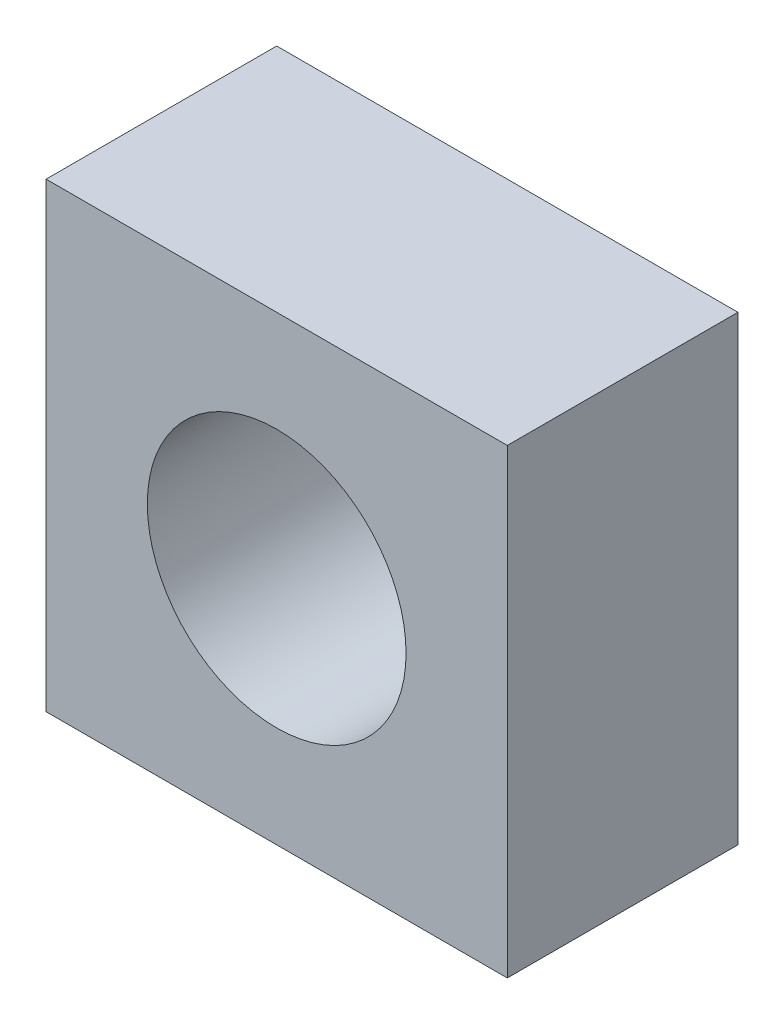
SolidWorks part; units mm, degrees
ref_plane "Front Plane" through (0, 0, 0) normal (0, 0, 1) x (1, 0, 0)
ref_plane "Top Plane" through (0, 0, 0) normal (0, 1, 0) x (1, 0, 0)
ref_plane "Right Plane" through (0, 0, 0) normal (1, 0, 0) x (0, 0, -1)
sketch "Sketch1" plane through (0, 0, 0) normal (0, 0, 1) x (1, 0, 0)
  line L1 (-20, -20) -> (20, -20)
  line L2 (-20, -20) -> (-20, 20)
  line L3 (-20, 20) -> (20, 20)
  line L4 (20, -20) -> (20, 20)
  line L5 (0, 20) -> (0, -20) construction
  line L6 (-20, 0) -> (20, 0) construction
  circle A0 centre (0, 0) radius 11.2192
  dimension "D1" = 40
  dimension "D2" = 40
extrude "Boss-Extrude1" add sketch "Sketch1" along normal blind 20
